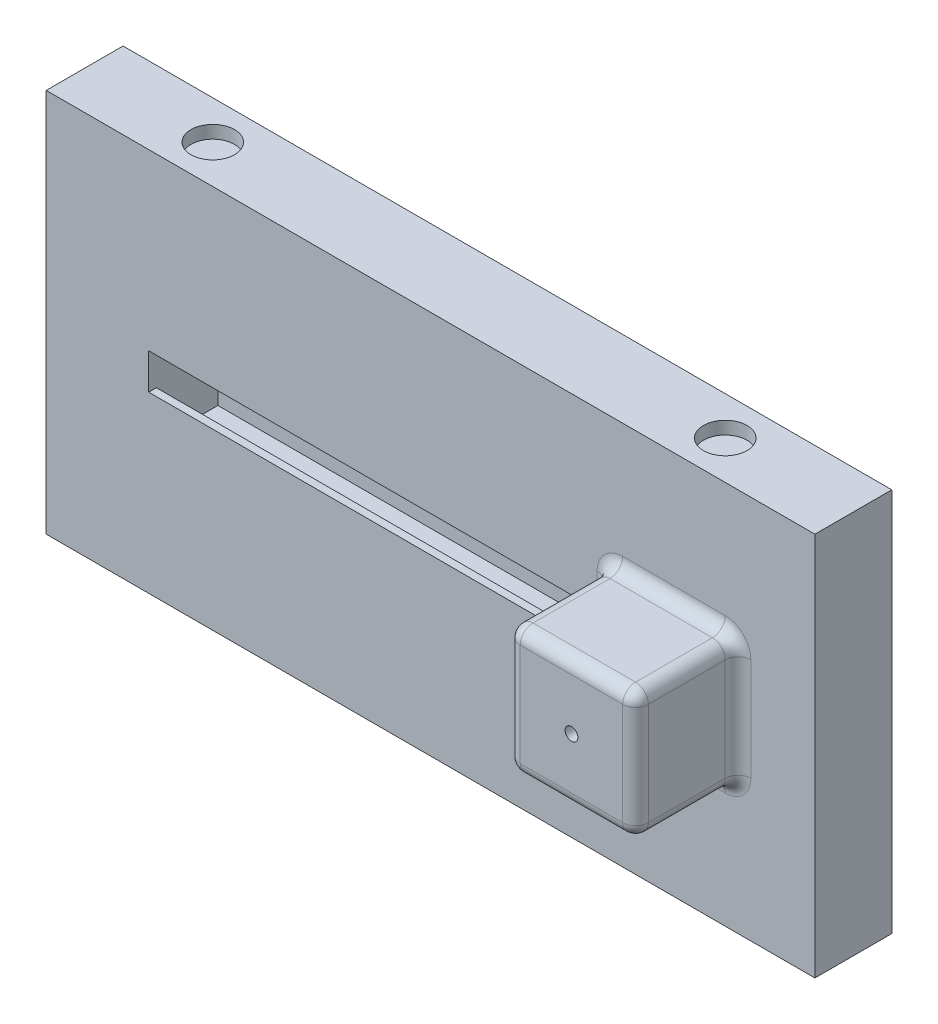
SolidWorks part; units mm, degrees
ref_plane "Front Plane" through (0, 0, 0) normal (0, 0, 1) x (1, 0, 0)
ref_plane "Top Plane" through (0, 0, 0) normal (0, 1, 0) x (1, 0, 0)
ref_plane "Right Plane" through (0, 0, 0) normal (1, 0, 0) x (0, 0, -1)
sketch "Sketch1" plane through (0, 0, 0) normal (0, 0, 1) x (1, 0, 0)
  line L1 (-150, -75) -> (150, -75)
  line L2 (-150, -75) -> (-150, 75)
  line L3 (-150, 75) -> (150, 75)
  line L4 (150, -75) -> (150, 75)
  line L5 (-150, -75) -> (150, 75) construction
  line L6 (-150, 75) -> (150, -75) construction
  line L7 (-110, 25) -> (110, 25)
  line L8 (-110, 25) -> (-110, -25)
  line L9 (-110, -25) -> (110, -25)
  line L10 (110, 25) -> (110, -25)
  line L11 (-110, 25) -> (110, -25) construction
  line L12 (-110, -25) -> (110, 25) construction
  point P0 (0, 0)
  point P6 (0, 0)
  dimension "D1" = 300
  dimension "D2" = 150
  dimension "D3" = 220
  dimension "D4" = 50
extrude "Boss-Extrude2" add sketch "Sketch1" along normal mid plane 30
ref_plane "Plane1" through (0, 0, 15) normal (0, 0, 1) x (1, 0, 0)
sketch "Sketch2" plane through (0, 0, 15) normal (0, 0, 1) x (1, 0, 0)
  line L5 (110, -25) -> (110, 25) construction
  line L6 (-110, 25) -> (110, 25)
  line L9 (-110, 25) -> (-110, 7)
  line L10 (-110, 7) -> (110, 7)
  line L11 (110, 25) -> (110, 7)
  dimension "D1" = 18
extrude "Boss-Extrude3" add sketch "Sketch2" against normal blind 3
mirror "Mirror1" about plane through (0, 0, 0) normal (0, 0, 1) of "Boss-Extrude3"
mirror "Mirror2" about plane through (0, 0, 0) normal (0, 1, 0) of "Mirror1", "Boss-Extrude3"
ref_plane "Plane2" through (0, 0, -15) normal (0, 0, -1) x (-1, 0, 0)
sketch "Sketch3" plane through (0, 0, -15) normal (0, 0, -1) x (-1, 0, 0)
  line L1 (110, -7) -> (-110, -7)
  line L2 (110, -7) -> (110, 7)
  line L3 (110, 7) -> (-110, 7)
  line L4 (-110, -7) -> (-110, 7)
extrude "Boss-Extrude4" add sketch "Sketch3" against normal blind 2
ref_plane "Plane4" through (0, 75, 0) normal (0, 1, 0) x (1, 0, 0)
sketch "Sketch5" plane through (0, 75, 0) normal (0, 1, 0) x (1, 0, 0)
  circle A0 centre (-100, 0) radius 8.5
  circle A1 centre (100, 0) radius 8.5
  dimension "D2" = 17
  dimension "D1" = 100
  dimension "D3" = 100
extrude "Cut-Extrude2" cut sketch "Sketch5" against normal blind 5
mirror "Mirror3" about plane through (0, 0, 0) normal (0, 1, 0) of "Cut-Extrude2"
sketch "Sketch6" plane through (0, 0, 15) normal (0, 0, 1) x (1, 0, 0)
  line L1 (70, -25) -> (120, -25)
  line L2 (70, -25) -> (70, 25)
  line L3 (70, 25) -> (120, 25)
  line L4 (120, -25) -> (120, 25)
  line L5 (70, -25) -> (120, 25) construction
  line L6 (70, 25) -> (120, -25) construction
  line L7 (16.5, 75) -> (-16.5, 75) construction
  circle A0 centre (95, 0) radius 2.5
  point P0 (95, 0)
  dimension "D5" = 5
  dimension "D1" = 50
  dimension "D2" = 50
  dimension "D3" = 70
  dimension "D4" = 50
extrude "Boss-Extrude5" add sketch "Sketch6" along normal blind 40
fillet "Fillet3" radius 5 13 edges at (120, 0, 15) (95, 25, 15) (120, 25, 35) (70, 25, 35) (70, -16, 15) (70, 16, 15) (95, -25, 15) (120, -25, 35) (70, -25, 35) (120, 0, 55) (95, 25, 55) (70, 0, 55) (95, -25, 55)
